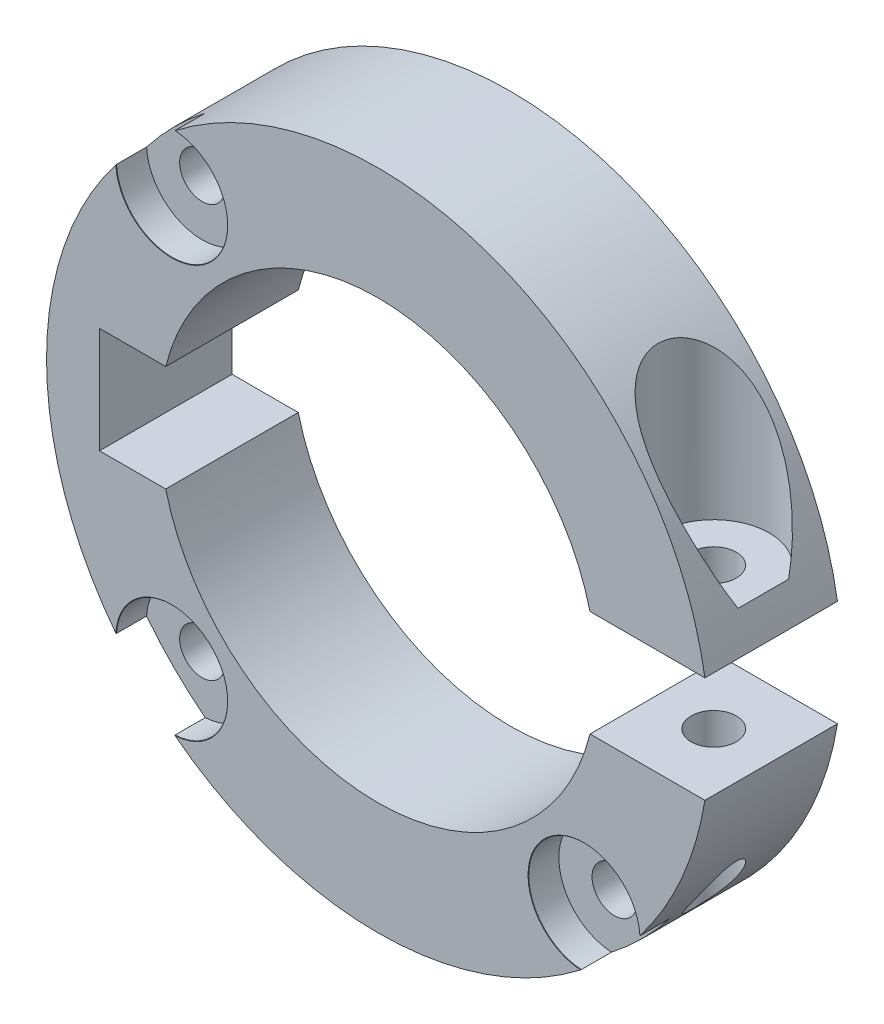
SolidWorks part; units mm, degrees
ref_plane "Front Plane" through (0, 0, 0) normal (0, 0, 1) x (1, 0, 0)
ref_plane "Top Plane" through (0, 0, 0) normal (0, 1, 0) x (1, 0, 0)
ref_plane "Right Plane" through (0, 0, 0) normal (1, 0, 0) x (0, 0, -1)
sketch "Sketch1" plane through (0, 0, 0) normal (0, 0, 1) x (1, 0, 0)
  line L0 (-25, 0) -> (25, 0) construction
  line L2 (-21, -4) -> (25, -4)
  line L3 (-21, -4) -> (-21, 4)
  line L4 (-21, 4) -> (25, 4)
  line L5 (25, -4) -> (25, 4)
  circle A0 centre (0, 0) radius 16.5
  circle A1 centre (0, 0) radius 25
  point P6 (0, 0)
  dimension "D1" = 33
  dimension "D2" = 50
  dimension "D3" = 8
  dimension "D4" = 21
extrude "Boss-Extrude1" add sketch "Sketch1" along normal blind 10 contours A1 L0 L3 L4 A0 | L0 A1 L2 A0 L3
sketch "Sketch2" plane through (0, 0, 10) normal (0, 0, 1) x (1, 0, 0)
  line L0 (-22, 0) -> (22, 0) construction
  line L1 (0, 0) -> (15.5563, 15.5563) construction
  line L2 (0, 0) -> (15.5563, -15.5563) construction
  line L3 (0, 0) -> (-15.5563, -15.5563) construction
  line L4 (0, 0) -> (-15.5563, 15.5563) construction
  circle A0 centre (0, 0) radius 22 construction
  arc A1 (24.6779, 4) -> (24.6779, -4) centre (0, 0) ccw construction
  point P8 (0, 0)
  point P16 (0, 0)
  dimension "D1" = 3
  dimension "D2" = 45
  dimension "D3" = 4
ref_plane "Plane1" through (0, 24, 0) normal (0, -1, 0) x (-1, 0, 0)
sketch "Sketch3" plane through (0, 24, 0) normal (0, -1, 0) x (-1, 0, 0)
  line L0 (-16.0078, 0) -> (-24.6779, -10) construction
  line L1 (-16.0078, -10) -> (-24.6779, 0) construction
  line L4 (-16.0078, 0) -> (-24.6779, 0)
  line L5 (-16.0078, -10) -> (-16.0078, 0)
  line L6 (-24.6779, -10) -> (-16.0078, -10)
  line L7 (-24.6779, 0) -> (-24.6779, -10)
  line L8 (-16.0078, 0) -> (-24.6779, 0)
  line L9 (-16.0078, -10) -> (-16.0078, 0)
  line L10 (-24.6779, -10) -> (-16.0078, -10)
  line L11 (-24.6779, 0) -> (-24.6779, -10)
  point P2 (-20.3429, -5)
  dimension "D1" = 0
hole_wizard "CBORE for M3 Hex Head Machine Screw2" positions "Sketch5" profile "Sketch6" counterbore size "M3" standard "ANSI Metric" end condition through all
sketch "Sketch5" plane through (0, 24, 0) normal (0, -1, 0) x (-1, 0, 0)
  point P0 (-20.3429, -5)
sketch "Sketch6" plane through (20.3429, 24, 5) normal (1, 0, 0) x (0, 0, 1)
  line L0 (0, 0) -> (0, 49)
  line L1 (0, 49) -> (1.7, 49)
  line L3 (1.7, 49) -> (1.7, 17.3)
  line L4 (4.2, 17.3) -> (1.7, 17.3)
  line L5 (4.2, 17.3) -> (4.2, 0.025)
  line L6 (4.2, 0.025) -> (4.225, 0)
  line L7 (4.225, 0) -> (0, 0)
  line L8 (-4.2, 0.025) -> (-4.225, 0) construction
  line L11 (0, -6.35) -> (0, 107.95) construction
  dimension "Thru Hole Dia." = 3.4
  dimension "Thru Hole Depth" = 49
  dimension "C'Bore Dia." = 8.4
  dimension "C'Bore Depth" = 17.3
  dimension "Near C'Sink Dia." = 8.45
  dimension "Near C'Sink Angle" = 90
hole_wizard "CBORE for M3 Hex Head Machine Screw3" positions "Sketch7" profile "Sketch8" counterbore size "M3" standard "ANSI Metric" end condition through all
sketch "Sketch7" plane through (-11.2763, -30.4367, 10) normal (0, 0, 1) x (1, 0, 0)
  point P3 (-4.2801, 45.993)
  point P6 (-4.2801, 14.8804)
  point P9 (26.8326, 14.8804)
  point P14 (0, 0)
sketch "Sketch8" plane through (-15.5563, 15.5563, 10) normal (1, 0, 0) x (0, -1, 0)
  line L0 (0, 0) -> (0, 10)
  line L1 (0, 10) -> (1.7, 10)
  line L2 (1.7, 10) -> (1.7, 2.3)
  line L3 (4.2, 2.3) -> (1.7, 2.3)
  line L4 (4.2, 2.3) -> (4.2, 0.025)
  line L5 (4.2, 0.025) -> (4.225, 0)
  line L6 (4.225, 0) -> (0, 0)
  line L7 (-4.2, 0.025) -> (-4.225, 0) construction
  line L8 (0, -6.35) -> (0, 107.95) construction
  dimension "Thru Hole Dia." = 3.4
  dimension "Thru Hole Depth" = 10
  dimension "C'Bore Dia." = 8.4
  dimension "C'Bore Depth" = 2.3
  dimension "Near C'Sink Dia." = 8.45
  dimension "Near C'Sink Angle" = 90
